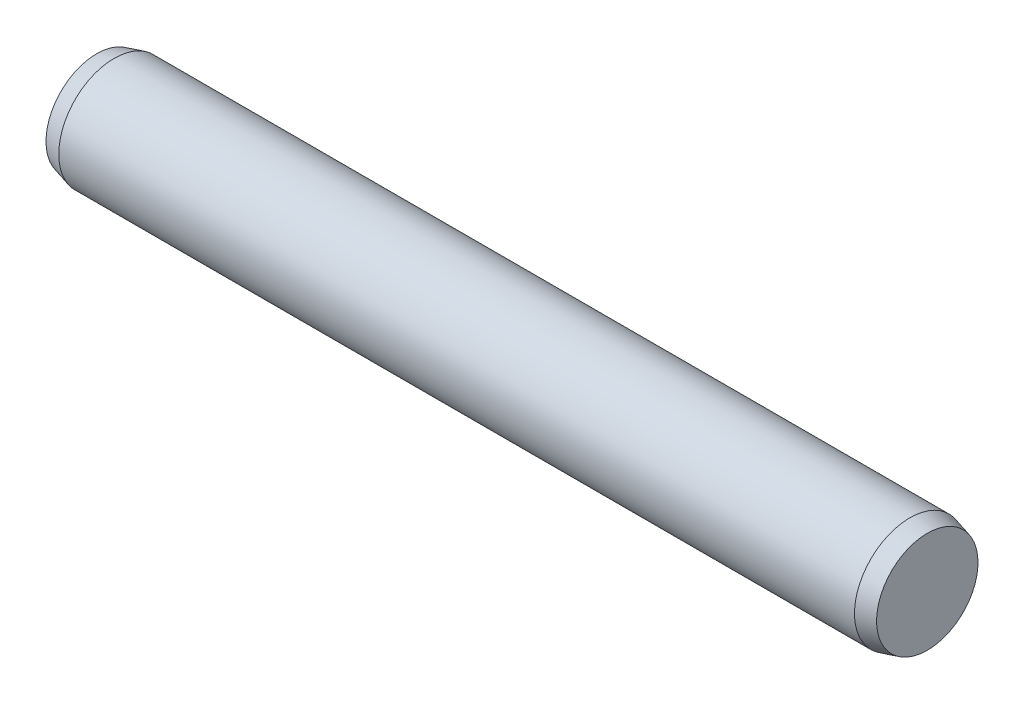
SolidWorks part; units mm, degrees
ref_plane "Front Plane" through (0, 0, 0) normal (0, 0, 1) x (1, 0, 0)
ref_plane "Top Plane" through (0, 0, 0) normal (0, 1, 0) x (1, 0, 0)
ref_plane "Right Plane" through (0, 0, 0) normal (1, 0, 0) x (0, 0, -1)
sketch "Sketch1" plane through (0, 0, 0) normal (0, 0, 1) x (1, 0, 0)
  line L0 (-14.37, 0) -> (14.37, 0) construction
  line L1 (14.37, 2) -> (14.37, -2) construction
  line L2 (-14.37, 2) -> (-14.37, -2) construction
  line L3 (15, 2) -> (15, -2) construction
  line L4 (-15, 2) -> (-15, -2) construction
  line L5 (-14.37, 0) -> (-15, 0) construction
  line L6 (14.37, 0) -> (15, 0) construction
  point P11 (11, 0)
  point P21 (-11, 0)
  dimension "Diameter" = 4
  dimension "Chamfer" = 0.63
  dimension "D1" = 0.63
  dimension "Length" = 30
  dimension "D2" = 4
  dimension "D3" = 4
sketch "Sketch2" plane through (0, 0, 0) normal (1, 0, 0) x (0, 0, -1)
  circle A0 centre (0, 0) radius 2
extrude "Extrude1" add sketch "Sketch2" against normal up to vertex (14.37 mm away) and the other way up to vertex (14.37 mm away) up to point (-14.37, 2, 0) other way up to point (14.37, 2, 0)
sketch "Sketch3" plane through (14.37, 0, 0) normal (1, 0, 0) x (0, 0, -1)
  circle A1 centre (0, 0) radius 2
  circle A2 centre (0, 0) radius 2
  dimension "D1" = 0
extrude "Extrude2" add sketch "Sketch3" along normal up to vertex (0.63 mm away) draft 15 up to point (15, 0, 0)
sketch "Sketch4" plane through (-14.37, 0, 0) normal (-1, 0, 0) x (0, 0, 1)
  circle A1 centre (0, 0) radius 2
  circle A2 centre (0, 0) radius 2
  dimension "D1" = 0
extrude "Extrude3" add sketch "Sketch4" along normal up to vertex (0.63 mm away) draft 15 up to point (-15, 0, 0)
sketch "Sketch5" plane through (0, 0, 0) normal (1, 0, 0) x (0, 0, -1)
  line L0 (-2, 0) -> (2, 0) construction
  point P4 (0, 0)
  dimension "D1" = 4
equation "\"D1@Sketch1\" = \"Chamfer@Sketch1\""
equation "\"D1@Sketch5\" = \"Diameter@Sketch1\""
equation "\"D2@Sketch1\" = \"Diameter@Sketch1\""
equation "\"D3@Sketch1\"=\"D2@Sketch1\""
